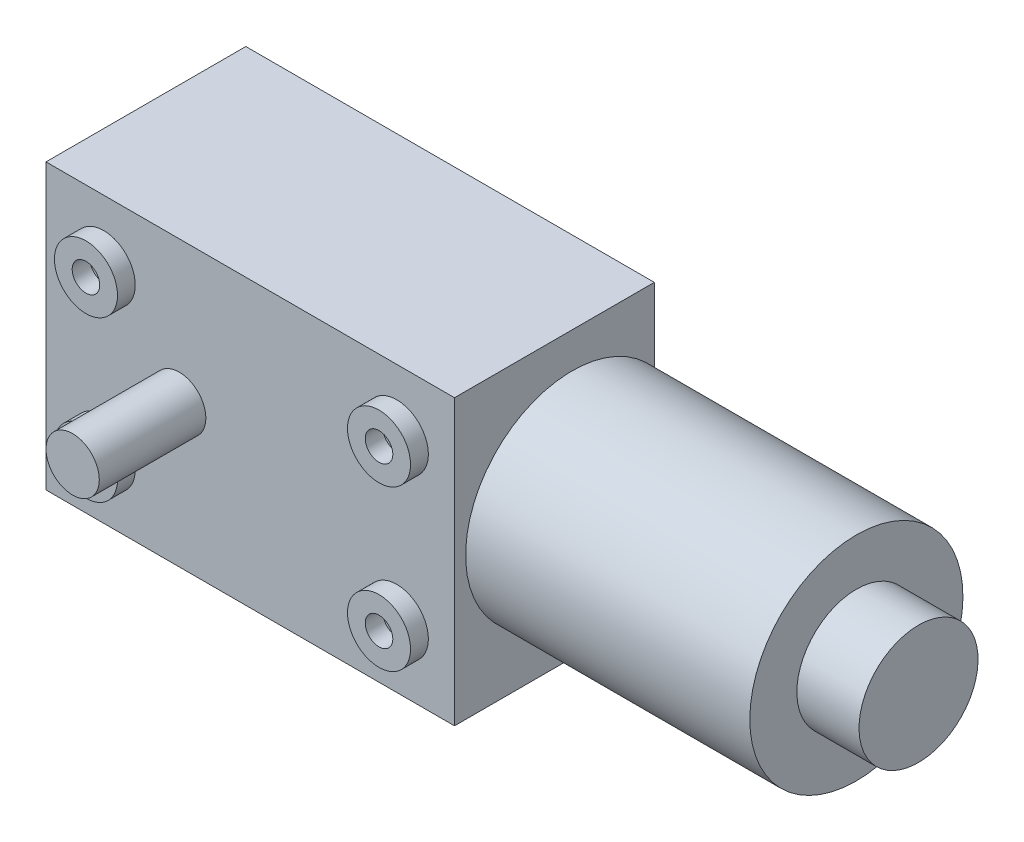
SolidWorks part; units mm, degrees
ref_plane "Front Plane" through (0, 0, 0) normal (0, 0, 1) x (1, 0, 0)
ref_plane "Top Plane" through (0, 0, 0) normal (0, 1, 0) x (1, 0, 0)
ref_plane "Right Plane" through (0, 0, 0) normal (1, 0, 0) x (0, 0, -1)
sketch "Sketch2" plane through (0, 0, 0) normal (0, 0, 1) x (1, 0, 0)
  line L1 (-23, 16) -> (23, 16)
  line L2 (-23, 16) -> (-23, -16)
  line L3 (-23, -16) -> (23, -16)
  line L4 (23, 16) -> (23, -16)
  dimension "D1" = 16
  dimension "D2" = 16
  dimension "D3" = 23
  dimension "D4" = 23
extrude "Boss-Extrude1" add sketch "Sketch2" along normal blind 22.5
sketch "Sketch3" plane through (0, 0, 22.5) normal (0, 0, 1) x (1, 0, 0)
  line L0 (-23, 16) -> (-23, -16) construction
  circle A0 centre (-8, 0) radius 3
  dimension "D2" = 6
  dimension "D1" = 15
extrude "Boss-Extrude2" add sketch "Sketch3" along normal blind 12
sketch "Sketch4" plane through (0, 0, 22.5) normal (0, 0, 1) x (1, 0, 0)
  line L0 (23, 16) -> (-23, 16) construction
  line L1 (-23, -16) -> (23, -16) construction
  line L2 (-23, 16) -> (-23, -16) construction
  circle A0 centre (-16.5, 9) radius 1.55
  circle A1 centre (-16.5, -9) radius 1.55
  circle A2 centre (-16.5, 9) radius 3.55
  circle A3 centre (-16.5, -9) radius 3.55
  circle A4 centre (16.5, -9) radius 3.55
  circle A5 centre (16.5, 9) radius 3.55
  circle A6 centre (16.5, -9) radius 1.55
  circle A7 centre (16.5, 9) radius 1.55
  dimension "D5" = 3.1
  dimension "D6" = 3.1
  dimension "D1" = 7
  dimension "D2" = 7
  dimension "D3" = 6.5
  dimension "D4" = 6.5
  dimension "D7" = 2
  dimension "D8" = 2
extrude "Boss-Extrude3" add sketch "Sketch4" along normal blind 2
sketch "Sketch5" plane through (23, 0, 0) normal (1, 0, 0) x (0, 0, -1)
  circle A0 centre (-9.25, 0) radius 12
  dimension "D1" = 9.25
extrude "Boss-Extrude4" add sketch "Sketch5" along normal blind 32
sketch "Sketch6" plane through (55, 0, 0) normal (1, 0, 0) x (0, 0, -1)
  circle A0 centre (-9.25, 0) radius 6.7
  dimension "D1" = 13.4
extrude "Boss-Extrude5" add sketch "Sketch6" along normal blind 7
